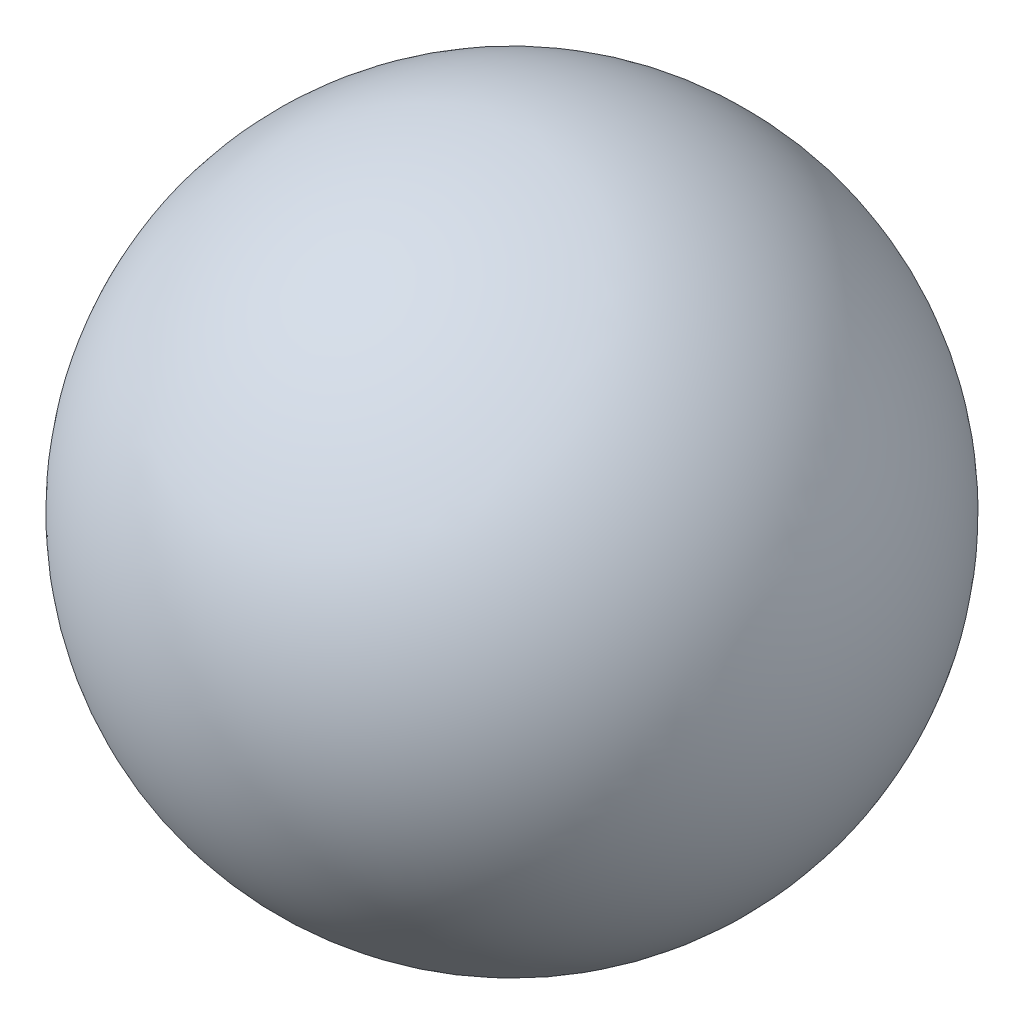
SolidWorks part; units mm, degrees
ref_plane "Front Plane" through (0, 0, 0) normal (0, 0, 1) x (1, 0, 0)
ref_plane "Top Plane" through (0, 0, 0) normal (0, 1, 0) x (1, 0, 0)
ref_plane "Right Plane" through (0, 0, 0) normal (1, 0, 0) x (0, 0, -1)
ref_plane "Plane1" through (0, 0, 0) normal (0, 0, 1) x (1, 0, 0)
sketch "Sketch1" plane through (0, 0, 0) normal (0, 0, 1) x (1, 0, 0)
  line L0 (6.8375, 7.325) -> (3.6625, 7.325)
  line L1 (6.8375, 7.325) -> (3.6625, 7.325) construction
  arc A0 (3.6625, 7.325) -> (6.8375, 7.325) centre (5.25, 7.325) cw
revolve "Revolve1" add sketch "Sketch1" angle 360 about L1
